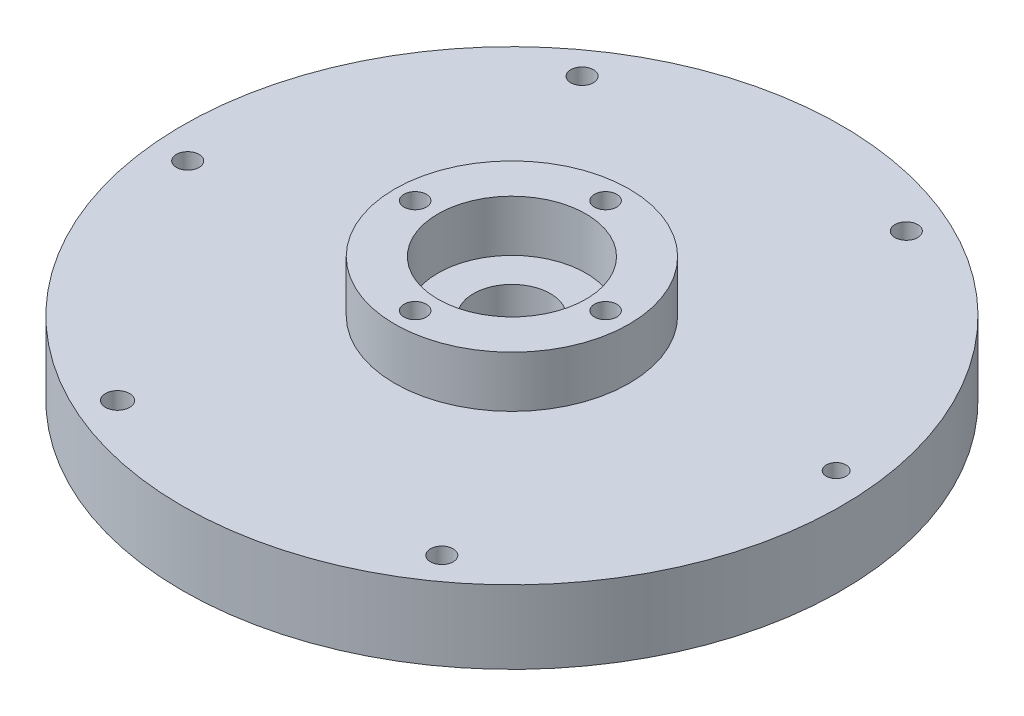
SolidWorks part; units mm, degrees
ref_plane "Front Plane" through (0, 0, 0) normal (0, 0, 1) x (1, 0, 0)
ref_plane "Top Plane" through (0, 0, 0) normal (0, 1, 0) x (1, 0, 0)
ref_plane "Right Plane" through (0, 0, 0) normal (1, 0, 0) x (0, 0, -1)
sketch "Sketch1" plane through (0, 0, 0) normal (0, 1, 0) x (1, 0, 0)
  circle A1 centre (0, 0) radius 45
  circle A2 centre (0, 0) radius 9.55
  circle A11 centre (23.5349, -33.114) radius 1.55
  circle A12 centre (-16.9101, -36.9388) radius 1.55
  circle A13 centre (-40.4451, -3.8248) radius 1.55
  circle A14 centre (-23.5349, 33.114) radius 1.55
  circle A15 centre (16.9101, 36.9388) radius 1.55
  circle A16 centre (40.4451, 3.8248) radius 1.55
  point P20 (0, 0)
  point P21 (0, 0)
  dimension "D1" = 3.1
  dimension "D2" = 90
  dimension "D4" = 6
extrude "Boss-Extrude1" add sketch "Sketch1" along normal blind 5
sketch "Sketch3" plane through (0, 5, 0) normal (0, 1, 0) x (1, 0, 0)
  circle A0 centre (0, 0) radius 45
  circle A1 centre (0, 0) radius 5.25
  circle A2 centre (16.9101, 36.9388) radius 1.55
  circle A3 centre (40.4451, 3.8248) radius 1.3477
  circle A4 centre (23.5349, -33.114) radius 1.55
  circle A5 centre (-16.9101, -36.9388) radius 1.6495
  circle A6 centre (-40.4451, -3.8248) radius 1.55
  circle A7 centre (-23.5349, 33.114) radius 1.55
  dimension "D1" = 10.5
extrude "Boss-Extrude2" add sketch "Sketch3" along normal blind 5
sketch "Sketch4" plane through (0, 10, 0) normal (0, 1, 0) x (1, 0, 0)
  circle A0 centre (0, 0) radius 10.1
  circle A1 centre (0, 0) radius 16
  dimension "D1" = 32
  dimension "D2" = 20.2
extrude "Boss-Extrude3" add sketch "Sketch4" along normal blind 7
sketch "Sketch5" plane through (0, 17, 0) normal (0, 1, 0) x (1, 0, 0)
  circle A0 centre (12.7866, 0) radius 1.525
  circle A2 centre (-0.2134, -13) radius 1.525
  circle A3 centre (-13.2134, 0) radius 1.525
  circle A4 centre (-0.2134, 13) radius 1.525
  point P2 (0, 0)
  point P3 (0, 0)
  point P11 (-0.2134, 0)
  dimension "D1" = 3.05
  dimension "D3" = 13
  dimension "D2" = 4
extrude "Cut-Extrude1" cut sketch "Sketch5" against normal blind 46
sketch "Sketch8" plane through (0, 0, 0) normal (0, -1, 0) x (1, 0, 0)
  circle A0 centre (-0.2134, -13) radius 3.2757
  circle A1 centre (-13, 0.2134) radius 3.2757
  circle A2 centre (0.2134, 13) radius 3.2757
  circle A3 centre (13, -0.2134) radius 3.2757
  point P12 (0, 0)
  dimension "D2" = 6.5515
  dimension "D1" = 4
extrude "Cut-Extrude4" cut sketch "Sketch8" against normal blind 7
